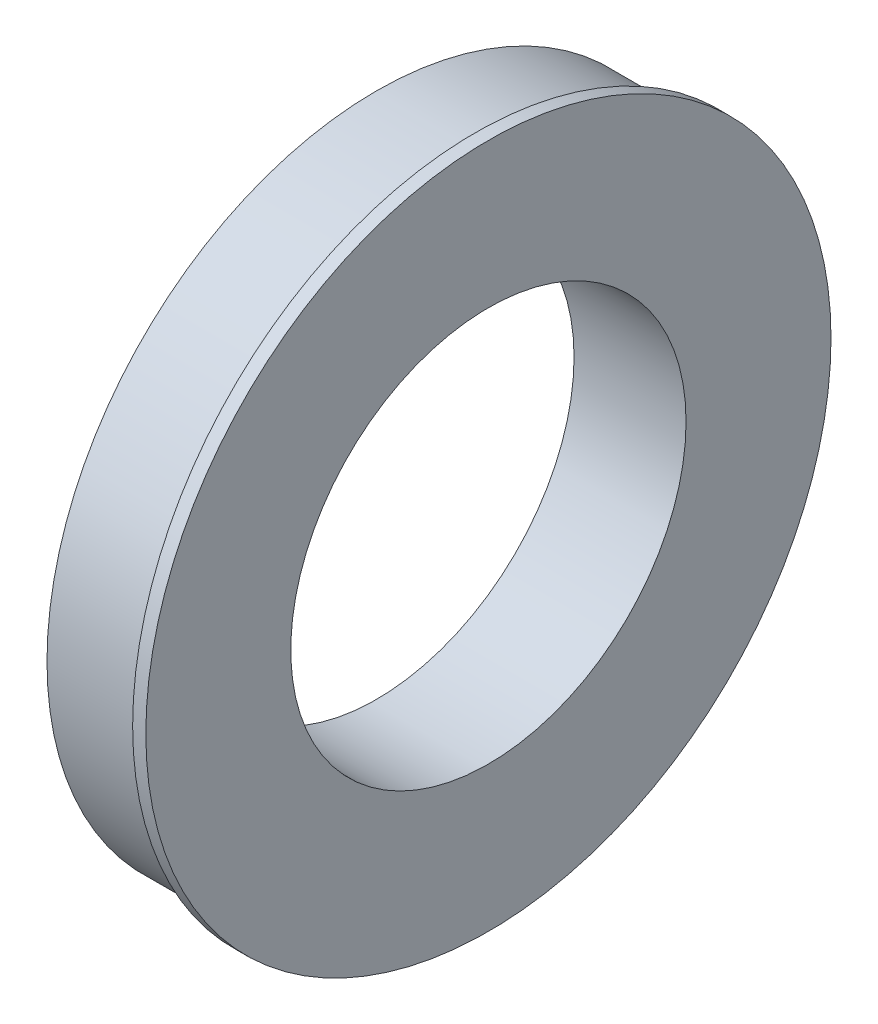
SolidWorks part; units mm, degrees
ref_plane "Front Plane" through (0, 0, 0) normal (0, 0, 1) x (1, 0, 0)
ref_plane "Top Plane" through (0, 0, 0) normal (0, 1, 0) x (1, 0, 0)
ref_plane "Right Plane" through (0, 0, 0) normal (1, 0, 0) x (0, 0, -1)
sketch "Sketch1" plane through (0, 0, 0) normal (1, 0, 0) x (0, 0, -1)
  circle A0 centre (0, 0) radius 38.1
  circle A1 centre (0, 0) radius 63.5
  dimension "D1" = 76.2
  dimension "D2" = 127
extrude "Boss-Extrude1" add sketch "Sketch1" along normal blind 19.05
sketch "Sketch2" plane through (19.05, 0, 0) normal (1, 0, 0) x (0, 0, -1)
  circle A1 centre (0, 0) radius 38.1
  circle A2 centre (0, 0) radius 66.04
  circle A3 centre (0, 0) radius 66.04
  dimension "D1" = 2.54
extrude "Boss-Extrude2" add sketch "Sketch2" along normal blind 2.54
